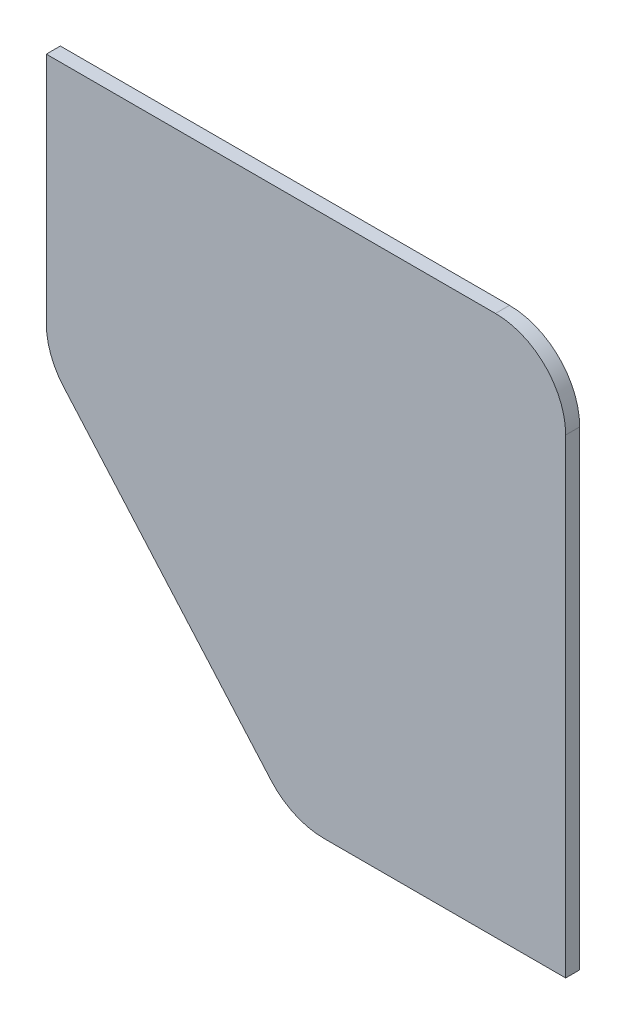
SolidWorks part; units mm, degrees
ref_plane "Plano frontal" through (0, 0, 0) normal (0, 0, 1) x (1, 0, 0)
ref_plane "Plano superior" through (0, 0, 0) normal (0, 1, 0) x (1, 0, 0)
ref_plane "Plano direito" through (0, 0, 0) normal (1, 0, 0) x (0, 0, -1)
sketch "Esboço1" plane through (0, 0, 0) normal (0, 0, 1) x (1, 0, 0)
  line L1 (-86.1657, 44.0263) -> (-12.1657, 44.0263)
  line L2 (-86.1657, 44.0263) -> (-86.1657, -32.9737)
  line L3 (-86.1657, -32.9737) -> (-12.1657, -32.9737)
  line L4 (-12.1657, 44.0263) -> (-12.1657, -32.9737)
  dimension "D1" = 77
  dimension "D2" = 74
extrude "Ressalto-extrusão1" add sketch "Esboço1" along normal blind 2
sketch "Esboço2" plane through (0, 0, 2) normal (0, 0, 1) x (1, 0, 0)
  line L0 (-51.1657, -32.9737) -> (-86.1657, 7.0263)
  line L1 (-86.1657, -32.9737) -> (-12.1657, -32.9737) construction
  line L2 (-86.1657, 44.0263) -> (-86.1657, -32.9737) construction
  dimension "D1" = 35
  dimension "D2" = 40
extrude "Corte-extrusão1" cut sketch "Esboço2" against normal through all and the other way through all
fillet "Filete1" radius 10 1 edges at (-86.1657, 7.0263, 1)
fillet "Filete2" radius 10 1 edges at (-51.1657, -32.9737, 1)
fillet "Filete3" radius 10 1 edges at (-12.1657, 44.0263, 1)
